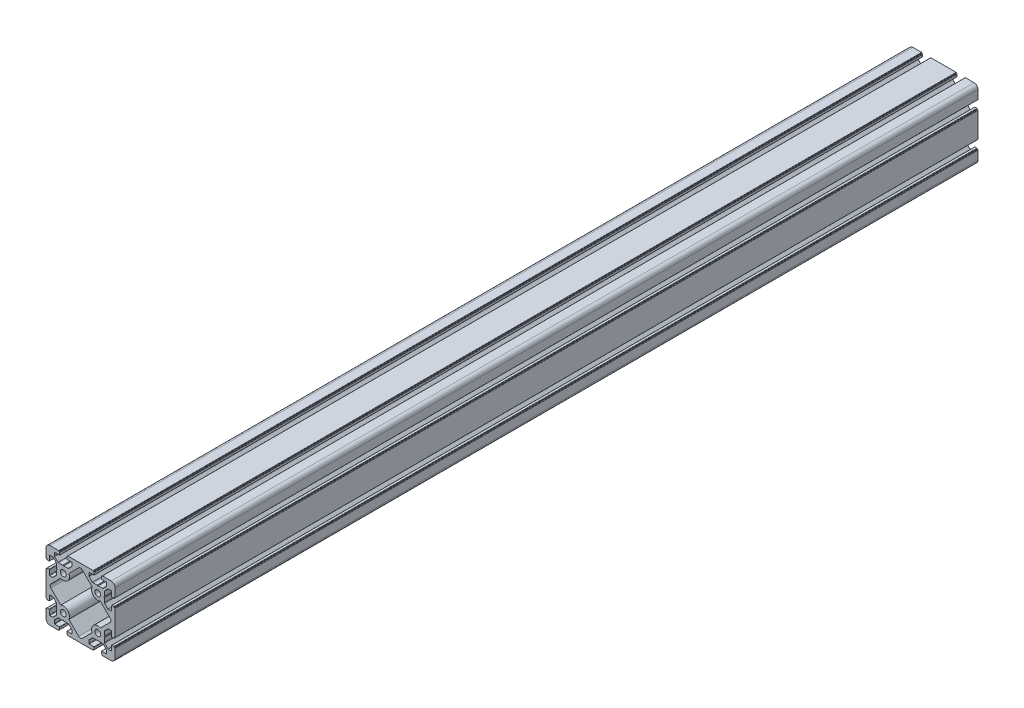
SolidWorks part; units mm, degrees
material "6063 T5"
ref_plane "Спереди" through (0, 0, 0) normal (0, 0, 1) x (1, 0, 0)
ref_plane "Сверху" through (0, 0, 0) normal (0, 1, 0) x (1, 0, 0)
ref_plane "Справа" through (0, 0, 0) normal (1, 0, 0) x (0, 0, -1)
sketch "Эскиз1" plane through (0, 0, 0) normal (0, 0, 1) x (1, 0, 0)
  line L0 (-20, 0) -> (0, 0) construction
  line L1 (0, 0) -> (0, 20) construction
  line L2 (-20, 0) -> (-20, 20) construction
  line L3 (-20, 20) -> (0, 20) construction
  line L4 (-39.9954, 50.3513) -> (40.0046, 50.3513) construction
  line L5 (-40, 30.25) -> (-40, 35.5)
  line L6 (-35.5, 40) -> (-30.25, 40)
  line L7 (-13.4648, 23.0219) -> (-2.1213, 34.3654)
  line L8 (-23.0219, 13.4648) -> (-34.3654, 2.1213)
  line L9 (13.4648, 23.0219) -> (2.1213, 34.3654)
  line L10 (23.0219, 13.4648) -> (34.3654, 2.1213)
  line L11 (-23.0219, -13.4648) -> (-34.3654, -2.1213)
  line L12 (-13.4648, -23.0219) -> (-2.1213, -34.3654)
  line L13 (13.4648, -23.0219) -> (2.1213, -34.3654)
  line L14 (23.0219, -13.4648) -> (34.3654, -2.1213)
  line L15 (30.25, 40) -> (35.5, 40)
  line L16 (40, 35.5) -> (40, 30.25)
  line L17 (40, -30.25) -> (40, -35.5)
  line L18 (35.5, -40) -> (30.25, -40)
  line L19 (-30.25, -40) -> (-35.5, -40)
  line L20 (-40, -35.5) -> (-40, -30.25)
  line L21 (-9.75, 40) -> (9.75, 40)
  line L22 (40, 9.75) -> (40, -9.75)
  line L23 (9.75, -40) -> (-9.75, -40)
  line L24 (-40, -9.75) -> (-40, 9.75)
  circle A0 centre (-20, 20) radius 3.4
  arc A1 (-40, 35.5) -> (-35.5, 40) centre (-35.5, 35.5) cw
  arc A2 (-23.0219, 13.4648) -> (-13.4648, 23.0219) centre (-20, 20) ccw
  arc A3 (23.0219, 13.4648) -> (13.4648, 23.0219) centre (20, 20) cw
  arc A4 (-23.0219, -13.4648) -> (-13.4648, -23.0219) centre (-20, -20) cw
  arc A5 (23.0219, -13.4648) -> (13.4648, -23.0219) centre (20, -20) ccw
  arc A6 (-2.1213, -34.3654) -> (2.1213, -34.3654) centre (0, -32.2441) ccw
  arc A7 (34.3654, 2.1213) -> (34.3654, -2.1213) centre (32.2441, 0) cw
  arc A8 (-34.3654, 2.1213) -> (-34.3654, -2.1213) centre (-32.2441, 0) ccw
  arc A9 (-2.1213, 34.3654) -> (2.1213, 34.3654) centre (0, 32.2441) cw
  arc A10 (35.5, 40) -> (40, 35.5) centre (35.5, 35.5) cw
  circle A11 centre (20, 20) radius 3.4
  arc A12 (40, -35.5) -> (35.5, -40) centre (35.5, -35.5) cw
  circle A13 centre (20, -20) radius 3.4
  arc A14 (-35.5, -40) -> (-40, -35.5) centre (-35.5, -35.5) cw
  circle A15 centre (-20, -20) radius 3.4
  point P36 (0, -36.4867)
  point P39 (36.4867, 0)
  point P42 (-36.4867, 0)
  point P45 (0, 36.4867)
  point P65 (0, 0)
  line B0 (-40, 30.25) -> (-40, 25.4)
  line B1 (-39.7, 25.1) -> (-39, 25.1)
  line B2 (-39, 25.1) -> (-39, 24.4)
  line B3 (-38.7, 24.1) -> (-36.3, 24.1)
  line B4 (-36, 24.4) -> (-36, 29.95)
  line B5 (-35.7, 30.25) -> (-32.3642, 30.25)
  line B6 (-31.6571, 29.9571) -> (-27.9929, 26.2929)
  line B7 (-27.7, 25.5858) -> (-27.7, 20.6)
  line B8 (-27.7, 20) -> (-40, 20) construction
  line B9 (-31.6571, 10.0429) -> (-27.9929, 13.7071)
  line B10 (-35.7, 9.75) -> (-32.3642, 9.75)
  line B11 (-36, 15.6) -> (-36, 10.05)
  line B12 (-38.7, 15.9) -> (-36.3, 15.9)
  line B13 (-39, 14.9) -> (-39, 15.6)
  line B14 (-39.7, 14.9) -> (-39, 14.9)
  line B15 (-40, 9.75) -> (-40, 14.6)
  line B16 (-27.7, 20.6) -> (-27.1, 20)
  line B17 (-27.1, 20) -> (-27.7, 19.4)
  line B18 (-27.7, 19.4) -> (-27.7, 14.4142)
  arc B19 (-36.3, 24.1) -> (-36, 24.4) centre (-36.3, 24.4) ccw
  arc B20 (-39, 24.4) -> (-38.7, 24.1) centre (-38.7, 24.4) ccw
  arc B21 (-40, 25.4) -> (-39.7, 25.1) centre (-39.7, 25.4) ccw
  arc B22 (-27.9929, 26.2929) -> (-27.7, 25.5858) centre (-28.7, 25.5858) cw
  arc B23 (-32.3642, 30.25) -> (-31.6571, 29.9571) centre (-32.3642, 29.25) cw
  arc B24 (-32.3642, 9.75) -> (-31.6571, 10.0429) centre (-32.3642, 10.75) ccw
  arc B25 (-27.9929, 13.7071) -> (-27.7, 14.4142) centre (-28.7, 14.4142) ccw
  arc B26 (-40, 14.6) -> (-39.7, 14.9) centre (-39.7, 14.6) cw
  arc B27 (-39, 15.6) -> (-38.7, 15.9) centre (-38.7, 15.6) cw
  arc B28 (-36.3, 15.9) -> (-36, 15.6) centre (-36.3, 15.6) cw
  arc B29 (-35.7, 9.75) -> (-36, 10.05) centre (-35.7, 10.05) cw
  arc B30 (-36, 29.95) -> (-35.7, 30.25) centre (-35.7, 29.95) cw
  line B31 (-9.75, 40) -> (-14.6, 40)
  line B32 (-14.9, 39.7) -> (-14.9, 39)
  line B33 (-14.9, 39) -> (-15.6, 39)
  line B34 (-15.9, 38.7) -> (-15.9, 36.3)
  line B35 (-15.6, 36) -> (-10.05, 36)
  line B36 (-9.75, 35.7) -> (-9.75, 32.3642)
  line B37 (-10.0429, 31.6571) -> (-13.7071, 27.9929)
  line B38 (-14.4142, 27.7) -> (-19.4, 27.7)
  line B39 (-20, 27.7) -> (-20, 40) construction
  line B40 (-29.9571, 31.6571) -> (-26.2929, 27.9929)
  line B41 (-30.25, 35.7) -> (-30.25, 32.3642)
  line B42 (-24.4, 36) -> (-29.95, 36)
  line B43 (-24.1, 38.7) -> (-24.1, 36.3)
  line B44 (-25.1, 39) -> (-24.4, 39)
  line B45 (-25.1, 39.7) -> (-25.1, 39)
  line B46 (-30.25, 40) -> (-25.4, 40)
  line B47 (-19.4, 27.7) -> (-20, 27.1)
  line B48 (-20, 27.1) -> (-20.6, 27.7)
  line B49 (-20.6, 27.7) -> (-25.5858, 27.7)
  arc B50 (-15.9, 36.3) -> (-15.6, 36) centre (-15.6, 36.3) ccw
  arc B51 (-15.6, 39) -> (-15.9, 38.7) centre (-15.6, 38.7) ccw
  arc B52 (-14.6, 40) -> (-14.9, 39.7) centre (-14.6, 39.7) ccw
  arc B53 (-13.7071, 27.9929) -> (-14.4142, 27.7) centre (-14.4142, 28.7) cw
  arc B54 (-9.75, 32.3642) -> (-10.0429, 31.6571) centre (-10.75, 32.3642) cw
  arc B55 (-30.25, 32.3642) -> (-29.9571, 31.6571) centre (-29.25, 32.3642) ccw
  arc B56 (-26.2929, 27.9929) -> (-25.5858, 27.7) centre (-25.5858, 28.7) ccw
  arc B57 (-25.4, 40) -> (-25.1, 39.7) centre (-25.4, 39.7) cw
  arc B58 (-24.4, 39) -> (-24.1, 38.7) centre (-24.4, 38.7) cw
  arc B59 (-24.1, 36.3) -> (-24.4, 36) centre (-24.4, 36.3) cw
  arc B60 (-30.25, 35.7) -> (-29.95, 36) centre (-29.95, 35.7) cw
  arc B61 (-10.05, 36) -> (-9.75, 35.7) centre (-10.05, 35.7) cw
  line B62 (40, 9.75) -> (40, 14.6)
  line B63 (39.7, 14.9) -> (39, 14.9)
  line B64 (39, 14.9) -> (39, 15.6)
  line B65 (38.7, 15.9) -> (36.3, 15.9)
  line B66 (36, 15.6) -> (36, 10.05)
  line B67 (35.7, 9.75) -> (32.3642, 9.75)
  line B68 (31.6571, 10.0429) -> (27.9929, 13.7071)
  line B69 (27.7, 14.4142) -> (27.7, 19.4)
  line B70 (27.7, 20) -> (40, 20) construction
  line B71 (31.6571, 29.9571) -> (27.9929, 26.2929)
  line B72 (35.7, 30.25) -> (32.3642, 30.25)
  line B73 (36, 24.4) -> (36, 29.95)
  line B74 (38.7, 24.1) -> (36.3, 24.1)
  line B75 (39, 25.1) -> (39, 24.4)
  line B76 (39.7, 25.1) -> (39, 25.1)
  line B77 (40, 30.25) -> (40, 25.4)
  line B78 (27.7, 19.4) -> (27.1, 20)
  line B79 (27.1, 20) -> (27.7, 20.6)
  line B80 (27.7, 20.6) -> (27.7, 25.5858)
  arc B81 (36.3, 15.9) -> (36, 15.6) centre (36.3, 15.6) ccw
  arc B82 (39, 15.6) -> (38.7, 15.9) centre (38.7, 15.6) ccw
  arc B83 (40, 14.6) -> (39.7, 14.9) centre (39.7, 14.6) ccw
  arc B84 (27.9929, 13.7071) -> (27.7, 14.4142) centre (28.7, 14.4142) cw
  arc B85 (32.3642, 9.75) -> (31.6571, 10.0429) centre (32.3642, 10.75) cw
  arc B86 (32.3642, 30.25) -> (31.6571, 29.9571) centre (32.3642, 29.25) ccw
  arc B87 (27.9929, 26.2929) -> (27.7, 25.5858) centre (28.7, 25.5858) ccw
  arc B88 (40, 25.4) -> (39.7, 25.1) centre (39.7, 25.4) cw
  arc B89 (39, 24.4) -> (38.7, 24.1) centre (38.7, 24.4) cw
  arc B90 (36.3, 24.1) -> (36, 24.4) centre (36.3, 24.4) cw
  arc B91 (35.7, 30.25) -> (36, 29.95) centre (35.7, 29.95) cw
  arc B92 (36, 10.05) -> (35.7, 9.75) centre (35.7, 10.05) cw
  line B93 (30.25, 40) -> (25.4, 40)
  line B94 (25.1, 39.7) -> (25.1, 39)
  line B95 (25.1, 39) -> (24.4, 39)
  line B96 (24.1, 38.7) -> (24.1, 36.3)
  line B97 (24.4, 36) -> (29.95, 36)
  line B98 (30.25, 35.7) -> (30.25, 32.3642)
  line B99 (29.9571, 31.6571) -> (26.2929, 27.9929)
  line B100 (25.5858, 27.7) -> (20.6, 27.7)
  line B101 (20, 27.7) -> (20, 40) construction
  line B102 (10.0429, 31.6571) -> (13.7071, 27.9929)
  line B103 (9.75, 35.7) -> (9.75, 32.3642)
  line B104 (15.6, 36) -> (10.05, 36)
  line B105 (15.9, 38.7) -> (15.9, 36.3)
  line B106 (14.9, 39) -> (15.6, 39)
  line B107 (14.9, 39.7) -> (14.9, 39)
  line B108 (9.75, 40) -> (14.6, 40)
  line B109 (20.6, 27.7) -> (20, 27.1)
  line B110 (20, 27.1) -> (19.4, 27.7)
  line B111 (19.4, 27.7) -> (14.4142, 27.7)
  arc B112 (24.1, 36.3) -> (24.4, 36) centre (24.4, 36.3) ccw
  arc B113 (24.4, 39) -> (24.1, 38.7) centre (24.4, 38.7) ccw
  arc B114 (25.4, 40) -> (25.1, 39.7) centre (25.4, 39.7) ccw
  arc B115 (26.2929, 27.9929) -> (25.5858, 27.7) centre (25.5858, 28.7) cw
  arc B116 (30.25, 32.3642) -> (29.9571, 31.6571) centre (29.25, 32.3642) cw
  arc B117 (9.75, 32.3642) -> (10.0429, 31.6571) centre (10.75, 32.3642) ccw
  arc B118 (13.7071, 27.9929) -> (14.4142, 27.7) centre (14.4142, 28.7) ccw
  arc B119 (14.6, 40) -> (14.9, 39.7) centre (14.6, 39.7) cw
  arc B120 (15.6, 39) -> (15.9, 38.7) centre (15.6, 38.7) cw
  arc B121 (15.9, 36.3) -> (15.6, 36) centre (15.6, 36.3) cw
  arc B122 (9.75, 35.7) -> (10.05, 36) centre (10.05, 35.7) cw
  arc B123 (29.95, 36) -> (30.25, 35.7) centre (29.95, 35.7) cw
  line B124 (9.75, -40) -> (14.6, -40)
  line B125 (14.9, -39.7) -> (14.9, -39)
  line B126 (14.9, -39) -> (15.6, -39)
  line B127 (15.9, -38.7) -> (15.9, -36.3)
  line B128 (15.6, -36) -> (10.05, -36)
  line B129 (9.75, -35.7) -> (9.75, -32.3642)
  line B130 (10.0429, -31.6571) -> (13.7071, -27.9929)
  line B131 (14.4142, -27.7) -> (19.4, -27.7)
  line B132 (20, -27.7) -> (20, -40) construction
  line B133 (29.9571, -31.6571) -> (26.2929, -27.9929)
  line B134 (30.25, -35.7) -> (30.25, -32.3642)
  line B135 (24.4, -36) -> (29.95, -36)
  line B136 (24.1, -38.7) -> (24.1, -36.3)
  line B137 (25.1, -39) -> (24.4, -39)
  line B138 (25.1, -39.7) -> (25.1, -39)
  line B139 (30.25, -40) -> (25.4, -40)
  line B140 (19.4, -27.7) -> (20, -27.1)
  line B141 (20, -27.1) -> (20.6, -27.7)
  line B142 (20.6, -27.7) -> (25.5858, -27.7)
  arc B143 (15.9, -36.3) -> (15.6, -36) centre (15.6, -36.3) ccw
  arc B144 (15.6, -39) -> (15.9, -38.7) centre (15.6, -38.7) ccw
  arc B145 (14.6, -40) -> (14.9, -39.7) centre (14.6, -39.7) ccw
  arc B146 (13.7071, -27.9929) -> (14.4142, -27.7) centre (14.4142, -28.7) cw
  arc B147 (9.75, -32.3642) -> (10.0429, -31.6571) centre (10.75, -32.3642) cw
  arc B148 (30.25, -32.3642) -> (29.9571, -31.6571) centre (29.25, -32.3642) ccw
  arc B149 (26.2929, -27.9929) -> (25.5858, -27.7) centre (25.5858, -28.7) ccw
  arc B150 (25.4, -40) -> (25.1, -39.7) centre (25.4, -39.7) cw
  arc B151 (24.4, -39) -> (24.1, -38.7) centre (24.4, -38.7) cw
  arc B152 (24.1, -36.3) -> (24.4, -36) centre (24.4, -36.3) cw
  arc B153 (30.25, -35.7) -> (29.95, -36) centre (29.95, -35.7) cw
  arc B154 (10.05, -36) -> (9.75, -35.7) centre (10.05, -35.7) cw
  line B155 (40, -30.25) -> (40, -25.4)
  line B156 (39.7, -25.1) -> (39, -25.1)
  line B157 (39, -25.1) -> (39, -24.4)
  line B158 (38.7, -24.1) -> (36.3, -24.1)
  line B159 (36, -24.4) -> (36, -29.95)
  line B160 (35.7, -30.25) -> (32.3642, -30.25)
  line B161 (31.6571, -29.9571) -> (27.9929, -26.2929)
  line B162 (27.7, -25.5858) -> (27.7, -20.6)
  line B163 (27.7, -20) -> (40, -20) construction
  line B164 (31.6571, -10.0429) -> (27.9929, -13.7071)
  line B165 (35.7, -9.75) -> (32.3642, -9.75)
  line B166 (36, -15.6) -> (36, -10.05)
  line B167 (38.7, -15.9) -> (36.3, -15.9)
  line B168 (39, -14.9) -> (39, -15.6)
  line B169 (39.7, -14.9) -> (39, -14.9)
  line B170 (40, -9.75) -> (40, -14.6)
  line B171 (27.7, -20.6) -> (27.1, -20)
  line B172 (27.1, -20) -> (27.7, -19.4)
  line B173 (27.7, -19.4) -> (27.7, -14.4142)
  arc B174 (36.3, -24.1) -> (36, -24.4) centre (36.3, -24.4) ccw
  arc B175 (39, -24.4) -> (38.7, -24.1) centre (38.7, -24.4) ccw
  arc B176 (40, -25.4) -> (39.7, -25.1) centre (39.7, -25.4) ccw
  arc B177 (27.9929, -26.2929) -> (27.7, -25.5858) centre (28.7, -25.5858) cw
  arc B178 (32.3642, -30.25) -> (31.6571, -29.9571) centre (32.3642, -29.25) cw
  arc B179 (32.3642, -9.75) -> (31.6571, -10.0429) centre (32.3642, -10.75) ccw
  arc B180 (27.9929, -13.7071) -> (27.7, -14.4142) centre (28.7, -14.4142) ccw
  arc B181 (40, -14.6) -> (39.7, -14.9) centre (39.7, -14.6) cw
  arc B182 (39, -15.6) -> (38.7, -15.9) centre (38.7, -15.6) cw
  arc B183 (36.3, -15.9) -> (36, -15.6) centre (36.3, -15.6) cw
  arc B184 (35.7, -9.75) -> (36, -10.05) centre (35.7, -10.05) cw
  arc B185 (36, -29.95) -> (35.7, -30.25) centre (35.7, -29.95) cw
  line B186 (-40, -9.75) -> (-40, -14.6)
  line B187 (-39.7, -14.9) -> (-39, -14.9)
  line B188 (-39, -14.9) -> (-39, -15.6)
  line B189 (-38.7, -15.9) -> (-36.3, -15.9)
  line B190 (-36, -15.6) -> (-36, -10.05)
  line B191 (-35.7, -9.75) -> (-32.3642, -9.75)
  line B192 (-31.6571, -10.0429) -> (-27.9929, -13.7071)
  line B193 (-27.7, -14.4142) -> (-27.7, -19.4)
  line B194 (-27.7, -20) -> (-40, -20) construction
  line B195 (-31.6571, -29.9571) -> (-27.9929, -26.2929)
  line B196 (-35.7, -30.25) -> (-32.3642, -30.25)
  line B197 (-36, -24.4) -> (-36, -29.95)
  line B198 (-38.7, -24.1) -> (-36.3, -24.1)
  line B199 (-39, -25.1) -> (-39, -24.4)
  line B200 (-39.7, -25.1) -> (-39, -25.1)
  line B201 (-40, -30.25) -> (-40, -25.4)
  line B202 (-27.7, -19.4) -> (-27.1, -20)
  line B203 (-27.1, -20) -> (-27.7, -20.6)
  line B204 (-27.7, -20.6) -> (-27.7, -25.5858)
  arc B205 (-36.3, -15.9) -> (-36, -15.6) centre (-36.3, -15.6) ccw
  arc B206 (-39, -15.6) -> (-38.7, -15.9) centre (-38.7, -15.6) ccw
  arc B207 (-40, -14.6) -> (-39.7, -14.9) centre (-39.7, -14.6) ccw
  arc B208 (-27.9929, -13.7071) -> (-27.7, -14.4142) centre (-28.7, -14.4142) cw
  arc B209 (-32.3642, -9.75) -> (-31.6571, -10.0429) centre (-32.3642, -10.75) cw
  arc B210 (-32.3642, -30.25) -> (-31.6571, -29.9571) centre (-32.3642, -29.25) ccw
  arc B211 (-27.9929, -26.2929) -> (-27.7, -25.5858) centre (-28.7, -25.5858) ccw
  arc B212 (-40, -25.4) -> (-39.7, -25.1) centre (-39.7, -25.4) cw
  arc B213 (-39, -24.4) -> (-38.7, -24.1) centre (-38.7, -24.4) cw
  arc B214 (-36.3, -24.1) -> (-36, -24.4) centre (-36.3, -24.4) cw
  arc B215 (-35.7, -30.25) -> (-36, -29.95) centre (-35.7, -29.95) cw
  arc B216 (-36, -10.05) -> (-35.7, -9.75) centre (-35.7, -10.05) cw
  line B217 (-30.25, -40) -> (-25.4, -40)
  line B218 (-25.1, -39.7) -> (-25.1, -39)
  line B219 (-25.1, -39) -> (-24.4, -39)
  line B220 (-24.1, -38.7) -> (-24.1, -36.3)
  line B221 (-24.4, -36) -> (-29.95, -36)
  line B222 (-30.25, -35.7) -> (-30.25, -32.3642)
  line B223 (-29.9571, -31.6571) -> (-26.2929, -27.9929)
  line B224 (-25.5858, -27.7) -> (-20.6, -27.7)
  line B225 (-20, -27.7) -> (-20, -40) construction
  line B226 (-10.0429, -31.6571) -> (-13.7071, -27.9929)
  line B227 (-9.75, -35.7) -> (-9.75, -32.3642)
  line B228 (-15.6, -36) -> (-10.05, -36)
  line B229 (-15.9, -38.7) -> (-15.9, -36.3)
  line B230 (-14.9, -39) -> (-15.6, -39)
  line B231 (-14.9, -39.7) -> (-14.9, -39)
  line B232 (-9.75, -40) -> (-14.6, -40)
  line B233 (-20.6, -27.7) -> (-20, -27.1)
  line B234 (-20, -27.1) -> (-19.4, -27.7)
  line B235 (-19.4, -27.7) -> (-14.4142, -27.7)
  arc B236 (-24.1, -36.3) -> (-24.4, -36) centre (-24.4, -36.3) ccw
  arc B237 (-24.4, -39) -> (-24.1, -38.7) centre (-24.4, -38.7) ccw
  arc B238 (-25.4, -40) -> (-25.1, -39.7) centre (-25.4, -39.7) ccw
  arc B239 (-26.2929, -27.9929) -> (-25.5858, -27.7) centre (-25.5858, -28.7) cw
  arc B240 (-30.25, -32.3642) -> (-29.9571, -31.6571) centre (-29.25, -32.3642) cw
  arc B241 (-9.75, -32.3642) -> (-10.0429, -31.6571) centre (-10.75, -32.3642) ccw
  arc B242 (-13.7071, -27.9929) -> (-14.4142, -27.7) centre (-14.4142, -28.7) ccw
  arc B243 (-14.6, -40) -> (-14.9, -39.7) centre (-14.6, -39.7) cw
  arc B244 (-15.6, -39) -> (-15.9, -38.7) centre (-15.6, -38.7) cw
  arc B245 (-15.9, -36.3) -> (-15.6, -36) centre (-15.6, -36.3) cw
  arc B246 (-9.75, -35.7) -> (-10.05, -36) centre (-10.05, -35.7) cw
  arc B247 (-29.95, -36) -> (-30.25, -35.7) centre (-29.95, -35.7) cw
  dimension "D3" = 6.8
  dimension "D7" = 4.5
  dimension "D9" = 7.2
  dimension "D11" = 3
  dimension "D1" = 20
  dimension "D2" = 20
  dimension "D4" = 20
  dimension "D5" = 20
  dimension "D6" = 80
  dimension "D8" = 45
  dimension "D10" = 25.8
  dimension "D12" = 4
sketch_block_instance "8W(22,6P_cut)-1"
sketch_block "8W(22,6P_cut)" parameters "D7"=0.3, "D8"=1, "D12"=0.3, "D10"=0.3, "D1"=12.3, "D2"=4, "D3"=8.2, "D4"=20.5, "D5"=10.2, "D6"=135, "D9"=1, "D11"=2.5, "D13"=1.2, "D14"=11.8
sketch_block_instance "8W(22,6P_cut)-3"
sketch_block_instance "8W(22,6P_cut)-4"
sketch_block_instance "8W(22,6P_cut)-5"
sketch_block_instance "8W(22,6P_cut)-6"
sketch_block_instance "8W(22,6P_cut)-7"
sketch_block_instance "8W(22,6P_cut)-8"
sketch_block_instance "8W(22,6P_cut)-9"
extrude "Бобышка-Вытянуть1" add sketch "Эскиз1" along normal blind 1000 contours B245 B229 B244 B230 B231 B243 B232 L23 B124 B145 B125 B126 B144 B127 B143 B128 B154 B129 B147 B130 B146 B131 B140 B141 B142 B149 B133 B148 B134 B153 B135 B152 B136 B151 B137 B138 B150 B139 L18 A12 L17 B155 B176 B156 B157 B175 B158 B174 B159 B185 B160
